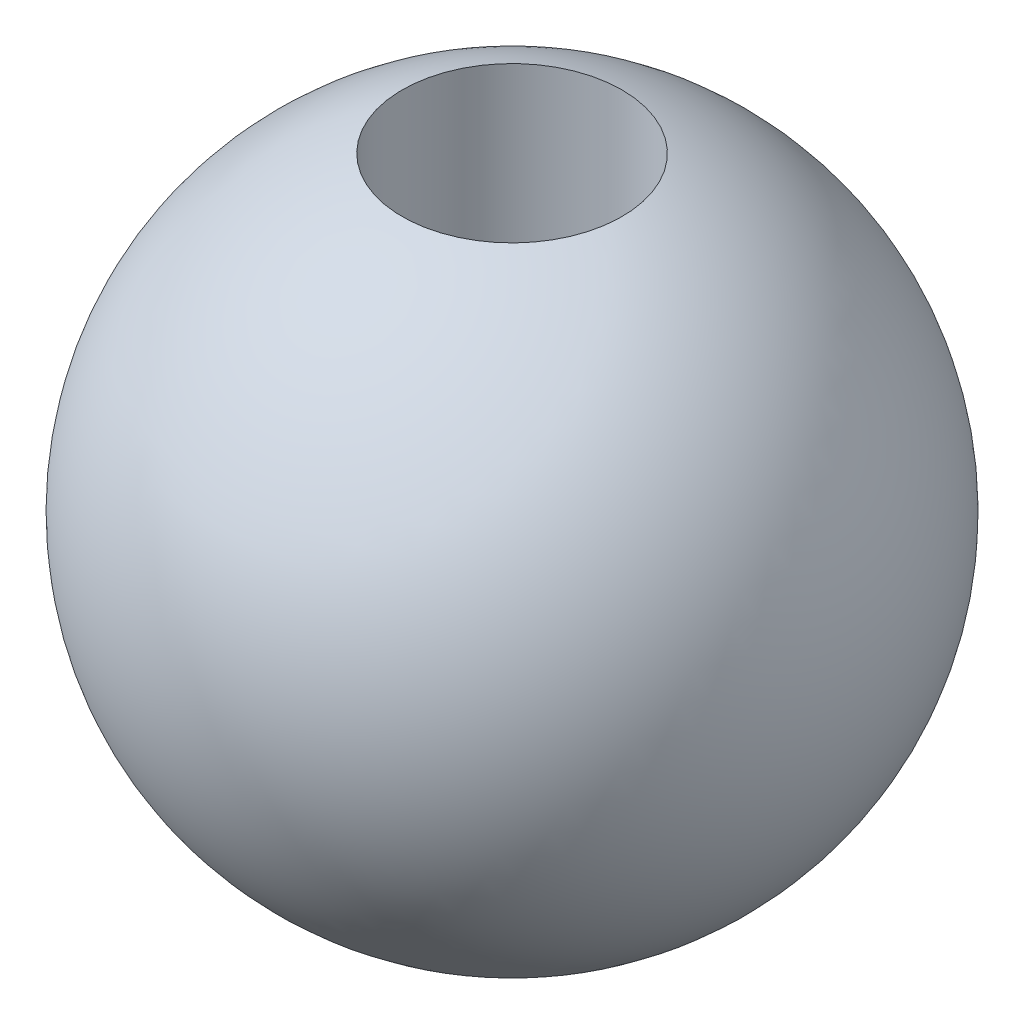
SolidWorks part; units mm, degrees
ref_plane "Front Plane" through (0, 0, 0) normal (0, 0, 1) x (1, 0, 0)
ref_plane "Top Plane" through (0, 0, 0) normal (0, 1, 0) x (1, 0, 0)
ref_plane "Right Plane" through (0, 0, 0) normal (1, 0, 0) x (0, 0, -1)
sketch "Sketch1" plane through (0, 0, 0) normal (0, 0, 1) x (1, 0, 0)
  line L0 (0, -1.5) -> (0, 1.5) construction
  line L1 (0.5, 1.4142) -> (0.5, -1.4142)
  arc A0 (0.5, -1.4142) -> (0.5, 1.4142) centre (0, 0) ccw
  dimension "D1" = 3
  dimension "D2" = 0.5
revolve "Revolve1" add sketch "Sketch1" angle 360 about L0
